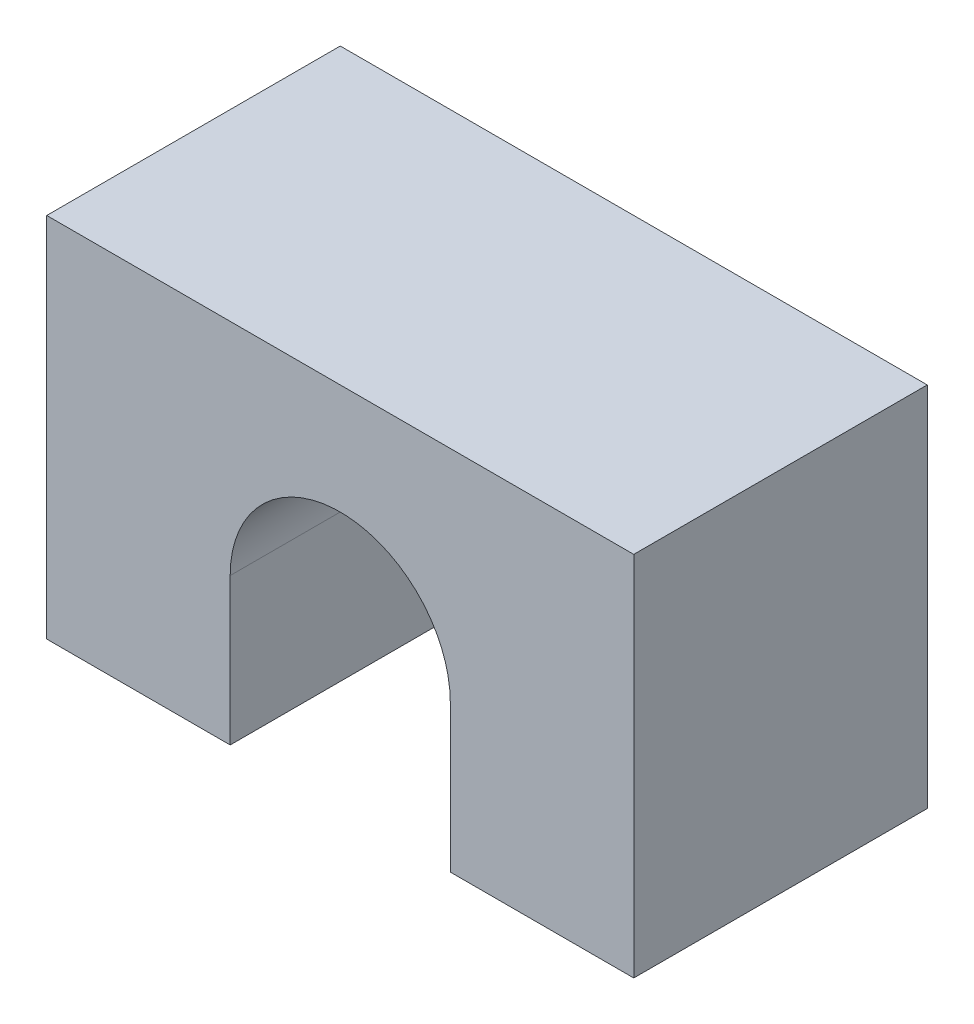
SolidWorks part; units mm, degrees
ref_plane "Front Plane" through (0, 0, 0) normal (0, 0, 1) x (1, 0, 0)
ref_plane "Top Plane" through (0, 0, 0) normal (0, 1, 0) x (1, 0, 0)
ref_plane "Right Plane" through (0, 0, 0) normal (1, 0, 0) x (0, 0, -1)
sketch "Sketch3" plane through (0, 0, 0) normal (0, 0, 1) x (1, 0, 0)
  line L0 (-10.8034, 0) -> (8.6235, 0) construction
  line L1 (0, 8.1471) -> (0, -8.2792) construction
  line L2 (-10.8034, 6) -> (8.6235, 6) construction
  line L3 (-8, 8.1471) -> (-8, -6.8108) construction
  line L4 (8, 8.1471) -> (8, -6.5225) construction
  line L5 (-11.0612, -4) -> (12.5753, -4) construction
  line L6 (-3, 0) -> (-3, -4)
  line L7 (3, 0) -> (3, -4)
  line L8 (3, -4) -> (8, -4)
  line L9 (8, -4) -> (8, 6)
  line L10 (8, 6) -> (-8, 6)
  line L11 (-8, 6) -> (-8, -4)
  line L12 (-8, -4) -> (-3, -4)
  arc A0 (3, 0) -> (-3, 0) centre (0, 0) ccw
  dimension "D1" = 6
  dimension "D2" = 6
  dimension "D3" = 8
  dimension "D4" = 8
  dimension "D5" = 4
extrude "Boss-Extrude1" add sketch "Sketch3" along normal blind 8
